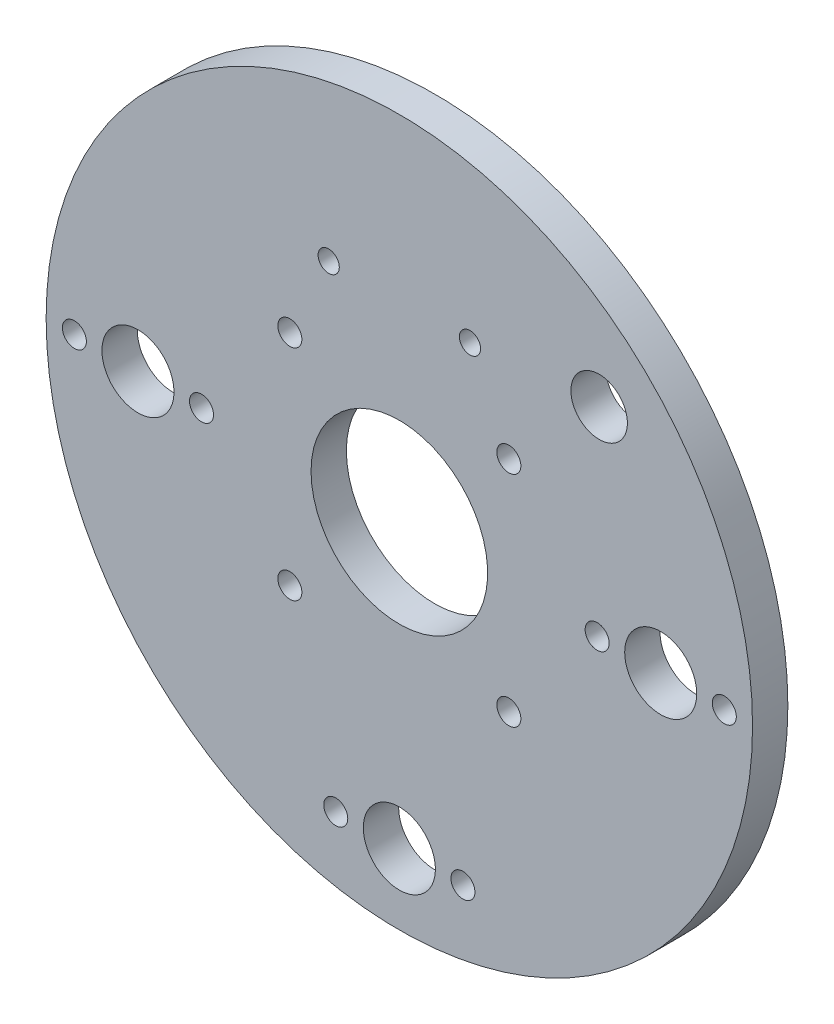
SolidWorks part; units mm, degrees
material "Acrylic (Medium-high impact)"
ref_plane "Front Plane" through (0, 0, 0) normal (0, 0, 1) x (1, 0, 0)
ref_plane "Top Plane" through (0, 0, 0) normal (0, 1, 0) x (1, 0, 0)
ref_plane "Right Plane" through (0, 0, 0) normal (1, 0, 0) x (0, 0, -1)
sketch "Sketch1" plane through (0, 0, 0) normal (0, 0, 1) x (1, 0, 0)
  circle A0 centre (0, 0) radius 50
  dimension "D1" = 100
extrude "Boss-Extrude1" add sketch "Sketch1" along normal blind 5
hole_wizard "Ø25.0 (25) Diameter Hole1" positions "Sketch3" profile "Sketch4" hole size "Ø25.0" standard "ISO" end condition through all
sketch "Sketch3" plane through (0, 0, 0) normal (0, 0, -1) x (-1, 0, 0)
  point P0 (0, 0)
sketch "Sketch4" plane through (0, 0, 0) normal (1, 0, 0) x (0, 1, 0)
  line L0 (0, 0) -> (0, 5)
  line L1 (0, 5) -> (12.5, 5)
  line L2 (12.5, 5) -> (12.5, 0)
  line L5 (12.5, 0) -> (0, 0)
  line L11 (0, -6.35) -> (0, 107.95) construction
  dimension "Thru Hole Dia." = 25
  dimension "Thru Hole Depth" = 5
hole_wizard "Ø10.2 (10.2) Diameter Hole1" positions "Sketch5" profile "Sketch6" hole size "Ø10.2" standard "ISO"
sketch "Sketch5" plane through (0, 0, 0) normal (0, 0, -1) x (-1, 0, 0)
  point P4 (37, 0)
  point P17 (-37, 0)
  point P18 (0, 0)
  point P21 (0, -37)
  point P23 (0, -40)
  dimension "D1" = 3
  dimension "D2" = 40
  dimension "D3" = 37
sketch "Sketch6" plane through (-37, 0, 0) normal (1, 0, 0) x (0, 1, 0)
  line L0 (0, 0) -> (0, 5)
  line L1 (0, 5) -> (5.1, 5)
  line L2 (5.1, 5) -> (5.1, 0)
  line L5 (5.1, 0) -> (0, 0)
  line L11 (0, -6.35) -> (0, 107.95) construction
  dimension "Thru Hole Dia." = 10.2
  dimension "Thru Hole Depth" = 5
hole_wizard "M3 Clearance Hole1" positions "Sketch7" profile "Sketch8" hole size "M3" standard "ISO" end condition through all
sketch "Sketch7" plane through (0, 0, 5) normal (0, 0, 1) x (1, 0, 0)
  circle A0 centre (37, 0) radius 5.1 construction
  circle A1 centre (0, -40) radius 5.1 construction
  point P0 (46, 0)
  point P2 (28, 0)
  point P11 (9, -40)
  point P13 (-9, -40)
  point P46 (-46, 0)
  point P47 (-28, 0)
  dimension "D2" = 9
  dimension "D1" = 9
  dimension "D4" = 9
  dimension "D5" = 9
  dimension "D6" = 2
  dimension "D3" = 40
sketch "Sketch8" plane through (46, 0, 5) normal (1, 0, 0) x (0, -1, 0)
  line L0 (0, 0) -> (0, 5)
  line L1 (0, 5) -> (1.7, 5)
  line L2 (1.7, 5) -> (1.7, 0)
  line L5 (1.7, 0) -> (0, 0)
  line L11 (0, -6.35) -> (0, 107.95) construction
  dimension "Thru Hole Dia." = 3.4
  dimension "Thru Hole Depth" = 5
hole_wizard "M3 Clearance Hole2" positions "Sketch9" profile "Sketch10" hole size "M3" standard "ISO" end condition through all
sketch "Sketch9" plane through (0, 0, 5) normal (0, 0, 1) x (1, 0, 0)
  point P0 (15.5, 15.5)
  point P22 (15.5, -15.5)
  point P23 (-15.5, -15.5)
  point P24 (-15.5, 15.5)
  dimension "D1" = 15.5
  dimension "D2" = 15.5
  dimension "D3" = 4
sketch "Sketch10" plane through (15.5, 15.5, 5) normal (1, 0, 0) x (0, -1, 0)
  line L0 (0, 0) -> (0, 5)
  line L1 (0, 5) -> (1.7, 5)
  line L2 (1.7, 5) -> (1.7, 0)
  line L5 (1.7, 0) -> (0, 0)
  line L11 (0, -6.35) -> (0, 107.95) construction
  dimension "Thru Hole Dia." = 3.4
  dimension "Thru Hole Depth" = 5
sketch "Sketch11" plane through (0, 0, 5) normal (0, 0, 1) x (1, 0, 0)
  circle A0 centre (-10, 27) radius 1.5
  circle A1 centre (10, 27) radius 1.5
  dimension "D1" = 3
  dimension "D2" = 3
  dimension "D3" = 10
  dimension "D4" = 10
  dimension "D5" = 27
  dimension "D6" = 27
extrude "Cut-Extrude1" cut sketch "Sketch11" against normal blind 10
sketch "Sketch12" plane through (0, 0, 5) normal (0, 0, 1) x (1, 0, 0)
  line L0 (0, 0) -> (28.2843, 28.2843) construction
  line L1 (0, 0) -> (21.8667, 0) construction
  circle A0 centre (28.2843, 28.2843) radius 4
  dimension "D1" = 40
  dimension "D3" = 8
  dimension "D2" = 45
extrude "Cut-Extrude2" cut sketch "Sketch12" against normal blind 10
